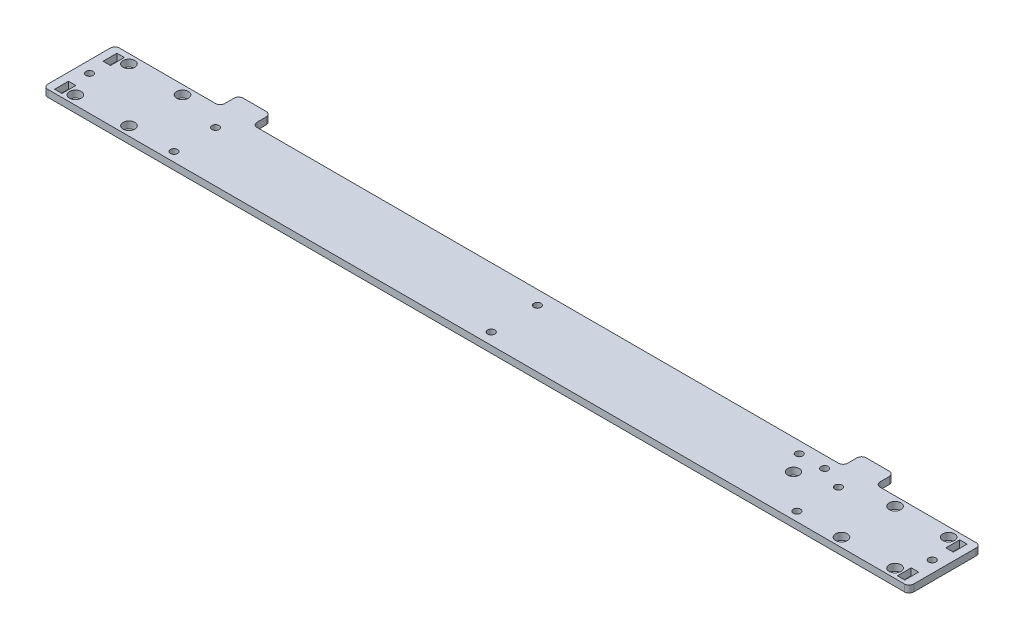
SolidWorks part; units mm, degrees
ref_plane "Alzado" through (0, 0, 0) normal (0, 0, 1) x (1, 0, 0)
ref_plane "Planta" through (0, 0, 0) normal (0, 1, 0) x (1, 0, 0)
ref_plane "Vista lateral" through (0, 0, 0) normal (1, 0, 0) x (0, 0, -1)
sketch "Croquis1" plane through (0, 0, 0) normal (0, 1, 0) x (1, 0, 0)
  line L0 (187.5, 31) -> (187.5, 0) construction
  line L1 (0, 0) -> (375, 0)
  line L2 (0, 0) -> (0, 31)
  line L3 (0, 31) -> (45.6, 31)
  line L4 (375, 0) -> (375, 31)
  line L5 (371.6, 1.5) -> (368.4, 1.5)
  line L6 (3.4, 28.5) -> (6.6, 28.5)
  line L7 (3.4, 28.5) -> (3.4, 22.5)
  line L8 (3.4, 22.5) -> (6.6, 22.5)
  line L9 (6.6, 28.5) -> (6.6, 22.5)
  line L10 (3.4, 7.5) -> (6.6, 7.5)
  line L11 (3.4, 7.5) -> (3.4, 1.5)
  line L12 (3.4, 1.5) -> (6.6, 1.5)
  line L13 (6.6, 7.5) -> (6.6, 1.5)
  line L14 (371.6, 7.5) -> (371.6, 1.5)
  line L15 (371.6, 7.5) -> (368.4, 7.5)
  line L16 (368.4, 7.5) -> (368.4, 1.5)
  line L17 (371.6, 22.5) -> (368.4, 22.5)
  line L18 (371.6, 28.5) -> (371.6, 22.5)
  line L19 (368.4, 28.5) -> (368.4, 22.5)
  line L20 (371.6, 28.5) -> (368.4, 28.5)
  line L21 (6.6, 31) -> (6.6, 0) construction
  line L22 (36.6, 31) -> (36.6, 0) construction
  line L23 (6.6, 0) -> (36.6, 31) construction
  line L24 (59.6, 31) -> (315.4, 31)
  line L25 (10, 27.1) -> (33.2, 27.1) construction
  line L26 (10, 27.1) -> (10, 3.9) construction
  line L27 (10, 3.9) -> (33.2, 3.9) construction
  line L28 (33.2, 27.1) -> (33.2, 3.9) construction
  line L29 (10, 27.1) -> (33.2, 3.9) construction
  line L30 (10, 3.9) -> (33.2, 27.1) construction
  line L32 (45.6, 31) -> (45.6, 39)
  line L33 (45.6, 39) -> (59.6, 39)
  line L34 (59.6, 31) -> (59.6, 39)
  line L35 (329.4, 31) -> (329.4, 39)
  line L36 (329.4, 39) -> (315.4, 39)
  line L37 (315.4, 31) -> (315.4, 39)
  line L38 (329.4, 31) -> (375, 31)
  line L39 (189, 31) -> (189, 0) construction
  line L40 (52.6, 39) -> (52.6, 0) construction
  line L41 (322.4, 39) -> (322.4, 0) construction
  line L42 (312.4, 26) -> (312.4, 8.2276) construction
  circle A0 centre (5, 15) radius 1.55
  circle A1 centre (370, 15) radius 1.55
  circle A2 centre (10, 27.1) radius 2.55
  circle A3 centre (33.2, 27.1) radius 2.55
  circle A4 centre (33.2, 3.9) radius 2.55
  circle A5 centre (10, 3.9) radius 2.55
  circle A6 centre (365, 3.9) radius 2.55
  circle A7 centre (341.8, 3.9) radius 2.55
  circle A8 centre (365, 27.1) radius 2.55
  circle A9 centre (341.8, 27.1) radius 2.55
  circle A10 centre (189, 25) radius 1.55
  circle A11 centre (189, 5) radius 1.55
  circle A12 centre (52.6, 22) radius 1.55
  circle A13 centre (52.6, 4) radius 1.55
  circle A14 centre (322.4, 22) radius 1.55
  circle A15 centre (322.4, 4) radius 1.55
  circle A16 centre (312.4, 26) radius 1.55
  circle A18 centre (301.4, 26) radius 1.55
  circle A20 centre (306.9, 18) radius 2.5
  point P31 (21.6, 15.5)
  dimension "D8" = 3.1
  dimension "D17" = 5.1
  dimension "D21" = 3.1
  dimension "D22" = 6
  dimension "D25" = 3.1
  dimension "D26" = 18
  dimension "D27" = 4
  dimension "D28" = 3.1
  dimension "D31" = 11
  dimension "D32" = 5
  dimension "D1" = 31
  dimension "D2" = 375
  dimension "D3" = 3.4
  dimension "D4" = 6
  dimension "D5" = 6
  dimension "D6" = 3.2
  dimension "D7" = 3.2
  dimension "D9" = 3.4
  dimension "D10" = 5
  dimension "D11" = 15
  dimension "D12" = 7.5
  dimension "D13" = 1.5
  dimension "D14" = 30
  dimension "D15" = 23.2
  dimension "D16" = 23.2
  dimension "D18" = 8
  dimension "D19" = 14
  dimension "D20" = 45.6
  dimension "D23" = 20
  dimension "D24" = 1.5
  dimension "D29" = 5
  dimension "D30" = 10
  dimension "D33" = 8
  dimension "D34" = 5.5
extrude "Saliente-Extruir1" add sketch "Croquis1" along normal blind 3
fillet "Redondeo2" radius 2 12 edges at (375, 1.5, 0) (375, 1.5, -31) (329.4, 1.5, -31) (329.4, 1.5, -39) (315.4, 1.5, -39) (315.4, 1.5, -31) (59.6, 1.5, -31) (59.6, 1.5, -39) (0, 1.5, 0) (45.6, 1.5, -39) (45.6, 1.5, -31) (0, 1.5, -31)
